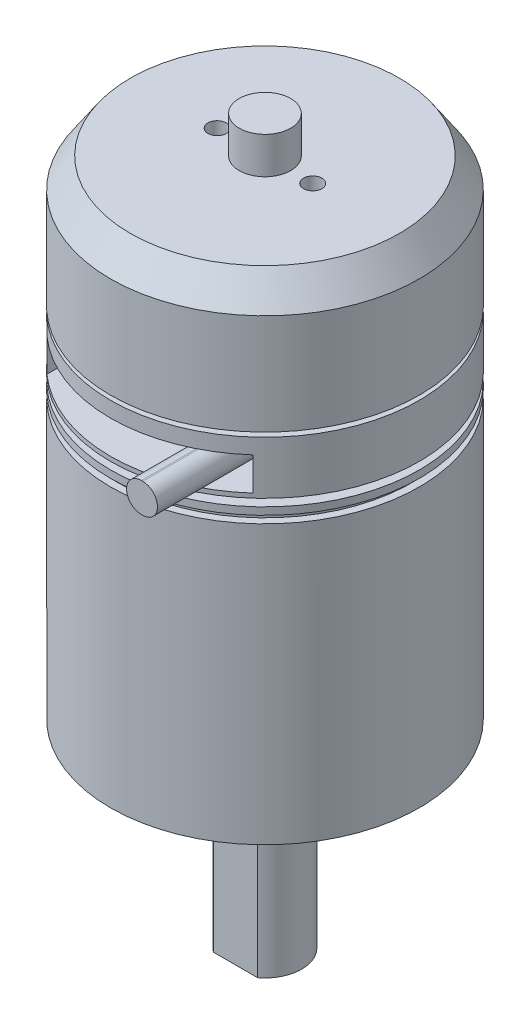
SolidWorks part; units mm, degrees
ref_plane "前视基准面" through (0, 0, 0) normal (0, 0, 1) x (1, 0, 0)
ref_plane "上视基准面" through (0, 0, 0) normal (0, 1, 0) x (1, 0, 0)
ref_plane "右视基准面" through (0, 0, 0) normal (1, 0, 0) x (0, 0, -1)
sketch "草图1" plane through (0, 0, 0) normal (0, 0, 1) x (1, 0, 0)
  line L0 (0, 0) -> (4.1, 0)
  line L1 (4.1, 0) -> (4.1, 6.7)
  line L2 (4.1, 6.7) -> (13.4, 6.7)
  line L3 (13.4, 6.7) -> (13.4, 8.7)
  line L4 (13.4, 8.7) -> (21, 8.7)
  line L5 (21, 8.7) -> (21, 10.2)
  line L6 (21, 10.2) -> (20, 10.2)
  line L7 (20, 10.2) -> (20, 11.2)
  line L8 (20, 11.2) -> (21, 11.2)
  line L9 (21, 11.2) -> (21, 12.2)
  line L10 (21, 12.2) -> (10, 12.2)
  line L11 (10, 12.2) -> (10, 13.2)
  line L12 (10, 13.2) -> (21, 13.2)
  line L13 (21, 13.2) -> (21, 20.4)
  line L14 (21, 20.4) -> (5, 20.4)
  line L15 (5, 20.4) -> (5, 21)
  line L16 (5, 21) -> (21, 21)
  line L17 (21, 21) -> (21, 34.7)
  line L18 (21, 34.7) -> (18.3, 38.7)
  line L19 (18.3, 38.7) -> (3.5, 38.7)
  line L20 (3.5, 38.7) -> (3.5, 43.7)
  line L21 (3.5, 43.7) -> (0, 43.7)
  line L22 (0, 43.7) -> (0, 0) construction
  line L23 (0, 0) -> (0, 43.7)
  dimension "D1" = 8.2
  dimension "D2" = 26.8
  dimension "D3" = 42
  dimension "D4" = 10
  dimension "D5" = 1.5
  dimension "D6" = 1
  dimension "D7" = 1
  dimension "D8" = 20
  dimension "D9" = 1
  dimension "D10" = 7.2
  dimension "D11" = 0.6
  dimension "D12" = 13.7
  dimension "D13" = 5
  dimension "D14" = 2
  dimension "D15" = 6.7
  dimension "D16" = 1
  dimension "D17" = 7
  dimension "D18" = 36.6
  dimension "D19" = 4
  dimension "D20" = 30
revolve "旋转1" add sketch "草图1" angle 360 about L22
ref_plane "基准面1" through (0, 0, 21) normal (0, 0, 1) x (1, 0, 0)
sketch "草图2" plane through (0, 0, 21) normal (0, 0, 1) x (1, 0, 0)
  line L1 (-14, 18.3) -> (14, 18.3)
  line L2 (-14, 18.3) -> (-14, 13.8)
  line L3 (-14, 13.8) -> (14, 13.8)
  line L4 (14, 18.3) -> (14, 13.8)
  line L5 (-14, 18.3) -> (14, 13.8) construction
  line L6 (-14, 13.8) -> (14, 18.3) construction
  line L7 (-21, 13.2) -> (21, 13.2) construction
  point P0 (0, 16.05)
  dimension "D1" = 28
  dimension "D2" = 4.5
  dimension "D3" = 0.6
extrude "切除-拉伸1" cut sketch "草图2" against normal blind 10
sketch "草图3" plane through (0, 0, 11) normal (0, 0, 1) x (1, 0, 0)
  line L0 (9.1851, 16.0532) -> (9.3851, 16.0532) construction
  line L1 (9.1851, 18.0532) -> (9.3851, 18.0532)
  line L2 (9.1851, 14.0532) -> (9.3851, 14.0532)
  arc A0 (9.1851, 18.0532) -> (9.1851, 14.0532) centre (9.1851, 16.0532) ccw
  arc A1 (9.3851, 14.0532) -> (9.3851, 18.0532) centre (9.3851, 16.0532) ccw
  point P2 (9.2851, 16.0532)
  dimension "D1" = 4
  dimension "D2" = 0.2
extrude "凸台-拉伸1" add sketch "草图3" along normal blind 15
hole_wizard "M3 螺纹孔1" positions "草图5" profile "草图6" tap size "M3" standard "GB"
sketch "草图5" plane through (0, 38.7, 0) normal (0, 1, 0) x (1, 0, 0)
  line L0 (0, 0) -> (0, 8.0606) construction
  point P0 (-6.5, 0)
  point P2 (6.5, 0)
  dimension "D1" = 13
sketch "草图6" plane through (-6.5, 38.7, 0) normal (1, 0, 0) x (0, 0, 1)
  line L0 (0, 0) -> (0, 4.7511)
  line L1 (0, 4.7511) -> (1.25, 4)
  line L2 (1.25, 4) -> (1.25, 0)
  line L5 (1.25, 0) -> (0, 0)
  line L10 (0, 4.7511) -> (-1.25, 4) construction
  line L11 (0, -6.35) -> (0, 107.95) construction
  dimension "螺纹孔钻头直径" = 2.5
  dimension "螺纹孔钻头深度" = 4
  dimension "导头角度" = 118
cosmetic thread "孔螺蚊线1" parameters "D1"=4, "D2"=3
cosmetic thread "孔螺蚊线2" parameters "D1"=4, "D2"=3
sketch "草图7" plane through (0, 0, 0) normal (0, 0, 1) x (1, 0, 0)
  line L0 (0, 8.7) -> (0, -54.6) construction
  line L1 (-13.4, 8.7) -> (13.4, 8.7) construction
  line L2 (0, -54.6) -> (5, -54.6)
  line L3 (5, -54.6) -> (5, -30.5)
  line L4 (5, -30.5) -> (8.275, -30.5)
  line L5 (13, -29.6) -> (13, -27.6)
  line L6 (13, -27.6) -> (21, -27.6)
  line L7 (21, -27.6) -> (21, 8.7)
  line L8 (-21, 8.7) -> (21, 8.7) construction
  line L9 (21, 8.7) -> (0, 8.7)
  line L10 (18.3, 38.7) -> (-18.3, 38.7) construction
  line L11 (13, -29.6) -> (8.275, -29.6)
  line L12 (8.275, -29.6) -> (8.275, -30.5)
  line L13 (0, 8.7) -> (0, -54.6)
  dimension "D1" = 66.3
  dimension "D2" = 2
  dimension "D3" = 0.9
  dimension "D4" = 27
  dimension "D5" = 26
  dimension "D6" = 10
  dimension "D7" = 16.55
revolve "旋转2" add sketch "草图7" angle 360 about L0
sketch "草图8" plane through (0, -54.6, 0) normal (0, -1, 0) x (1, 0, 0)
  line L0 (-3, 4) -> (3, 4)
  circle A0 centre (0, 0) radius 5 construction
  circle A1 centre (0, 0) radius 5 construction
  arc A2 (3, 4) -> (-3, 4) centre (0, 0) ccw
  dimension "D1" = 4
extrude "切除-拉伸2" cut sketch "草图8" against normal blind 20
hole_wizard "M4 螺纹孔1" positions "草图10" profile "草图9" tap size "M4" standard "GB"
sketch "草图10" plane through (0, -27.6, 0) normal (0, -1, 0) x (-1, 0, 0)
  circle A0 centre (0, 0) radius 17.5
  point P5 (0, -17.5)
  point P7 (-17.5, 0)
  point P9 (0, 17.5)
  point P11 (17.5, 0)
  dimension "D1" = 35
sketch "草图9" plane through (0, -27.6, 17.5) normal (1, 0, 0) x (0, 0, -1)
  line L0 (0, 0) -> (0, 11.0914)
  line L1 (0, 11.0914) -> (1.65, 10.1)
  line L2 (1.65, 10.1) -> (1.65, 0)
  line L5 (1.65, 0) -> (0, 0)
  line L10 (0, 11.0914) -> (-1.65, 10.1) construction
  line L11 (0, -6.35) -> (0, 107.95) construction
  dimension "螺纹孔钻头直径" = 3.3
  dimension "螺纹孔钻头深度" = 10.1
  dimension "导头角度" = 118
cosmetic thread "孔螺蚊线3" parameters "D1"=8, "D2"=4
cosmetic thread "孔螺蚊线4" parameters "D1"=8, "D2"=4
cosmetic thread "孔螺蚊线5" parameters "D1"=8, "D2"=4
cosmetic thread "孔螺蚊线6" parameters "D1"=8, "D2"=4
